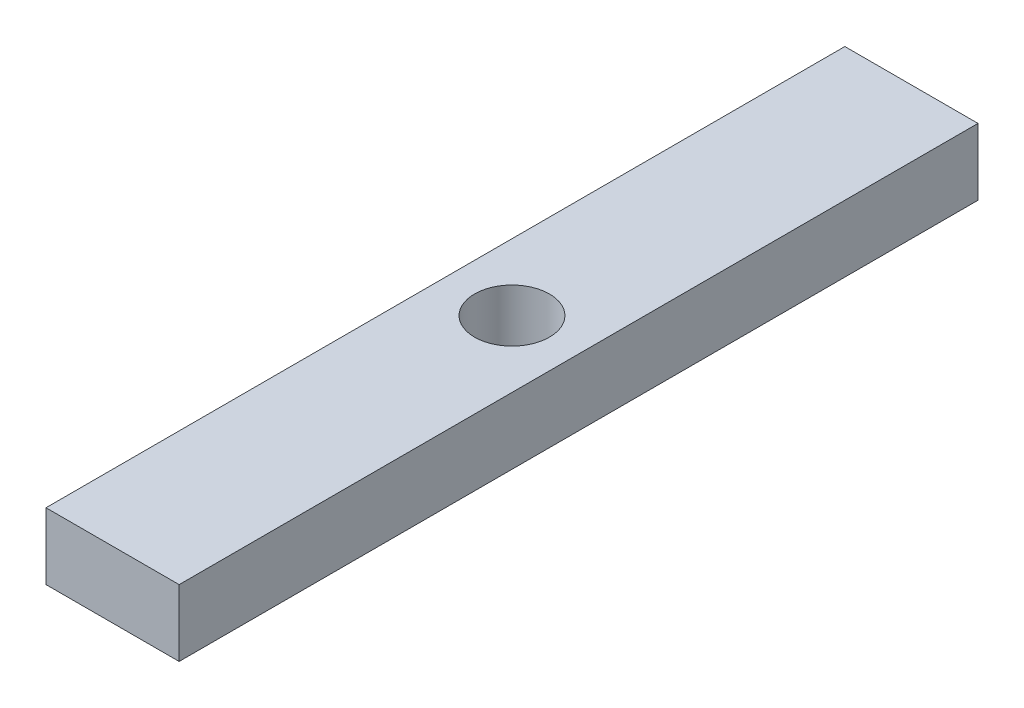
SolidWorks part; units mm, degrees
ref_plane "Front Plane" through (0, 0, 0) normal (0, 0, 1) x (1, 0, 0)
ref_plane "Top Plane" through (0, 0, 0) normal (0, 1, 0) x (1, 0, 0)
ref_plane "Right Plane" through (0, 0, 0) normal (1, 0, 0) x (0, 0, -1)
sketch "Sketch1" plane through (0, 0, 0) normal (0, 1, 0) x (1, 0, 0)
  line L1 (0, 0) -> (50.8, 0)
  line L2 (0, 0) -> (0, 304.8)
  line L3 (0, 304.8) -> (50.8, 304.8)
  line L4 (50.8, 0) -> (50.8, 304.8)
  circle A0 centre (25.4, 152.4) radius 14.2875
  point P7 (50.8, 152.4)
  point P10 (25.4, 304.8)
  dimension "D2" = 28.575
  dimension "D1" = 50.8
  dimension "D3" = 304.8
extrude "Boss-Extrude1" add sketch "Sketch1" along normal blind 25.4
